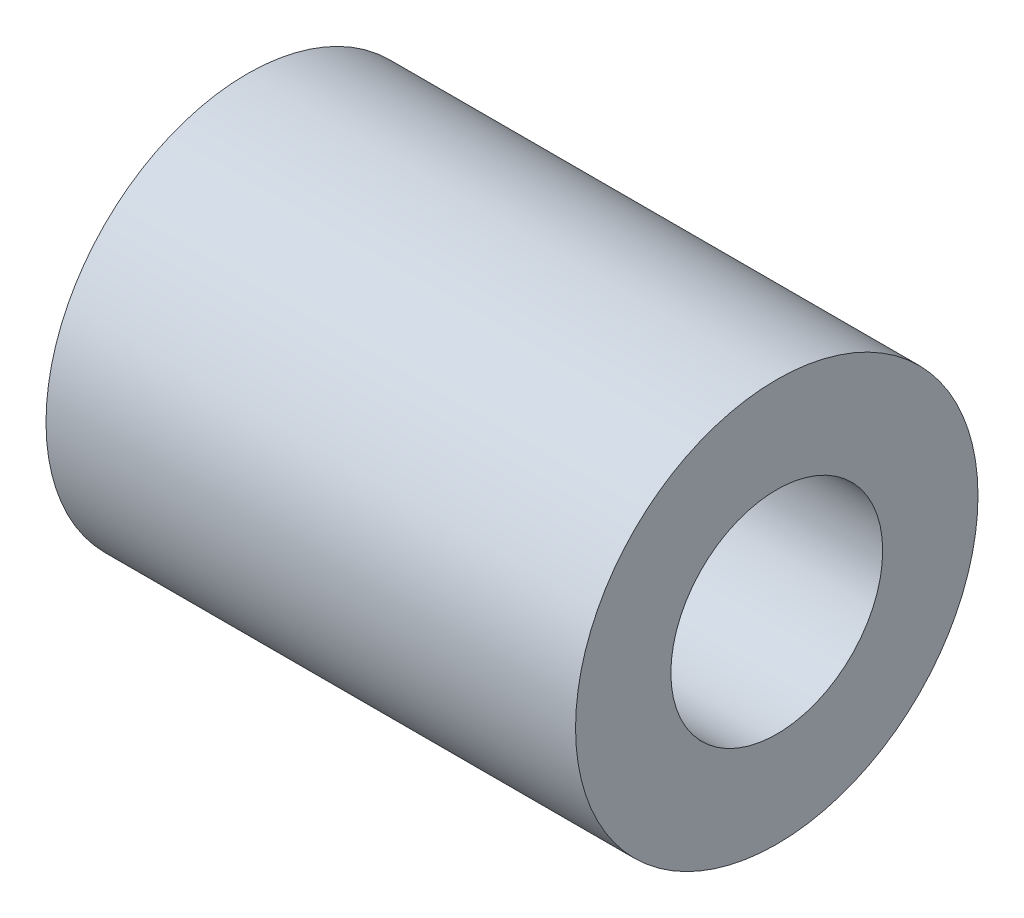
SolidWorks part; units mm, degrees
ref_plane "Ebene vorne" through (0, 0, 0) normal (0, 0, 1) x (1, 0, 0)
ref_plane "Ebene oben" through (0, 0, 0) normal (0, 1, 0) x (1, 0, 0)
ref_plane "Ebene rechts" through (0, 0, 0) normal (1, 0, 0) x (0, 0, -1)
sketch "Skizze2" plane through (0, 0, 0) normal (0, 0, 1) x (1, 0, 0)
  line L0 (0, 0) -> (13.7828, 0) construction
  line L1 (0, 2.5) -> (0, 9.5)
  line L2 (0, 9.5) -> (25, 9.5)
  line L3 (25, 9.5) -> (25, 5)
  line L4 (25, 5) -> (12.5, 5)
  line L5 (12.5, 5) -> (12.5, 2.5)
  line L6 (12.5, 2.5) -> (0, 2.5)
  dimension "D1" = 2.5
  dimension "D2" = 5
  dimension "D3" = 12.5
  dimension "D4" = 25
  dimension "D5" = 9.5
revolve "Rotation1" add sketch "Skizze2" angle 360 about L0
